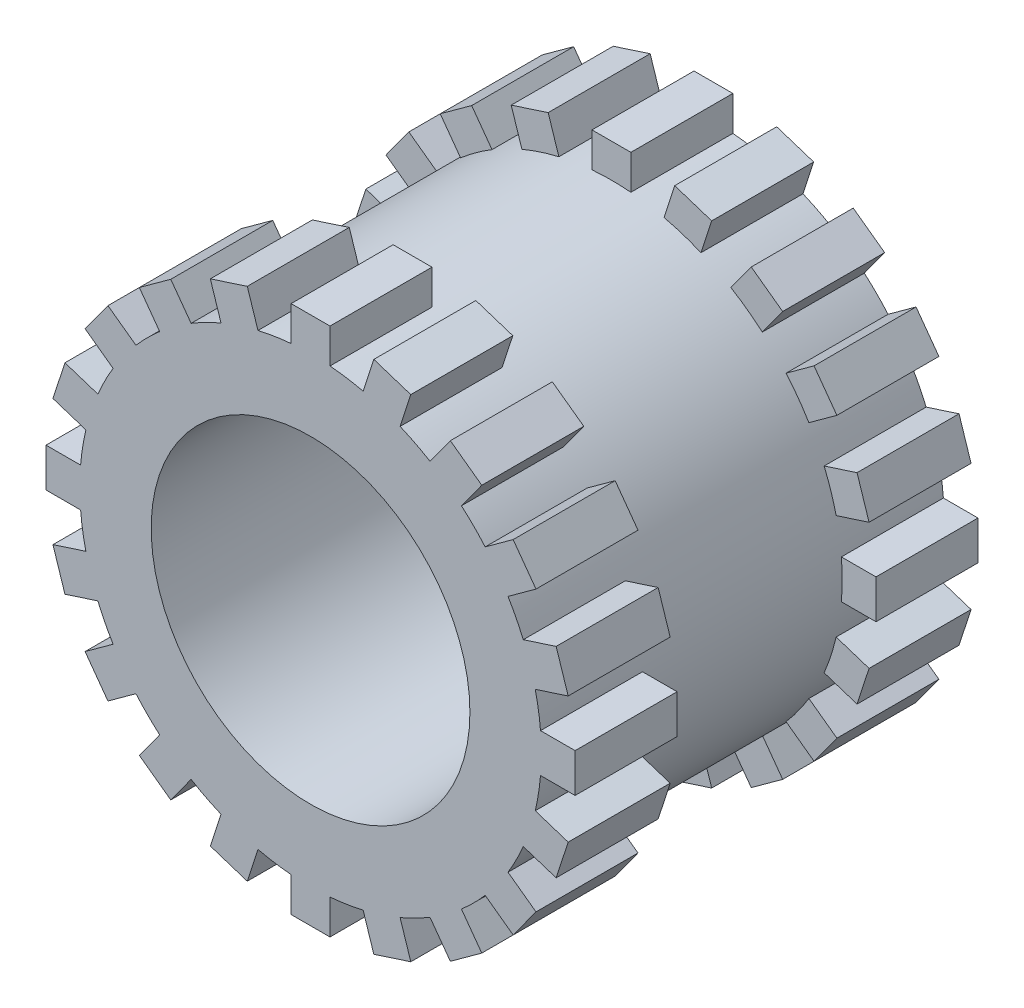
SolidWorks part; units mm, degrees
ref_plane "Front Plane" through (0, 0, 0) normal (0, 0, 1) x (1, 0, 0)
ref_plane "Top Plane" through (0, 0, 0) normal (0, 1, 0) x (1, 0, 0)
ref_plane "Right Plane" through (0, 0, 0) normal (1, 0, 0) x (0, 0, -1)
sketch "Sketch1" plane through (0, 0, 0) normal (0, 0, 1) x (1, 0, 0)
  circle A0 centre (0, 0) radius 1.81
  dimension "D1" = 3.62
extrude "Boss-Extrude1" add sketch "Sketch1" along normal mid plane 3.16
hole_wizard "Tap Drill for M3x0.5 Tap1" positions "Sketch2" profile "Sketch3" hole size "M3x0.5" standard "ANSI Metric" end condition through all
sketch "Sketch2" plane through (0, 0, 1.58) normal (0, 0, 1) x (1, 0, 0)
  point P0 (0, 0)
sketch "Sketch3" plane through (0, 0, 1.58) normal (1, 0, 0) x (0, -1, 0)
  line L0 (0, 0) -> (0, 3.16)
  line L1 (0, 3.16) -> (1.25, 3.16)
  line L2 (1.25, 3.16) -> (1.25, 0)
  line L5 (1.25, 0) -> (0, 0)
  line L11 (0, -6.35) -> (0, 107.95) construction
  dimension "Thru Hole Dia." = 2.5
  dimension "Thru Hole Depth" = 3.16
sketch "Sketch4" plane through (0, 0, 1.58) normal (0, 0, 1) x (1, 0, 0)
  line L0 (0, 2.075) -> (0, -2.075) construction
  line L1 (0.1524, 2.075) -> (-0.1524, 2.075)
  line L2 (-0.1524, 2.075) -> (-0.1524, 1.8036)
  line L3 (0.1524, 2.075) -> (0.1524, 1.8036)
  line L4 (0.1524, 1.8036) -> (-0.1524, 1.8036)
  circle A0 centre (0, 0) radius 1.81 construction
  dimension "D1" = 0.3048
  dimension "D2" = 4.15
extrude "Boss-Extrude2" add sketch "Sketch4" against normal blind 0.8
pattern_circular "CirPattern1" count 20 over 360 about axis through (0, 0, 0) along (0, 0, 1) of "Boss-Extrude2"
mirror "Mirror1" about plane through (0, 0, 0) normal (0, 0, 1) of "CirPattern1", "Boss-Extrude2"
